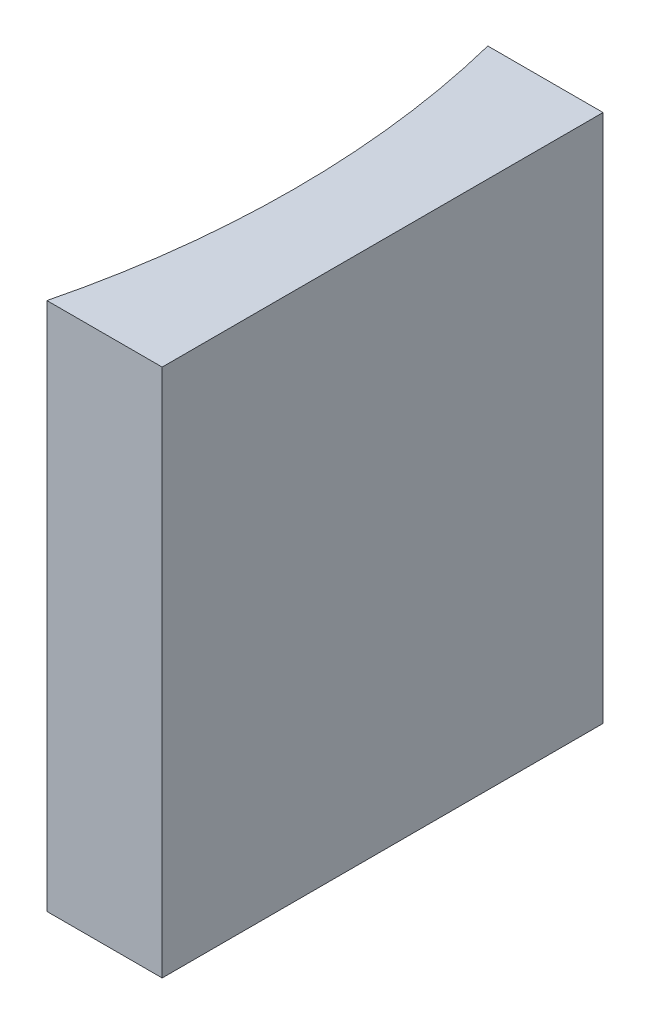
SolidWorks part; units mm, degrees
ref_plane "前视基准面" through (0, 0, 0) normal (0, 0, 1) x (1, 0, 0)
ref_plane "上视基准面" through (0, 0, 0) normal (0, 1, 0) x (1, 0, 0)
ref_plane "右视基准面" through (0, 0, 0) normal (1, 0, 0) x (0, 0, -1)
sketch "草图1" plane through (0, 0, 0) normal (0, 1, 0) x (1, 0, 0)
  line L0 (0, 0) -> (0, -10)
  line L1 (0, 0) -> (-2.6136, 0)
  line L2 (0, -10) -> (-2.6136, -10)
  line L3 (8.2336, -5) -> (-10.4405, -5) construction
  arc A0 (-2.6136, -10) -> (-2.6136, 0) centre (-22.68, -5) ccw
  point P7 (-2, -5)
  point P8 (0, -5)
  dimension "D2" = 20.68
  dimension "D3" = 2
  dimension "D1" = 10
extrude "凸台-拉伸1" add sketch "草图1" along normal blind 12
